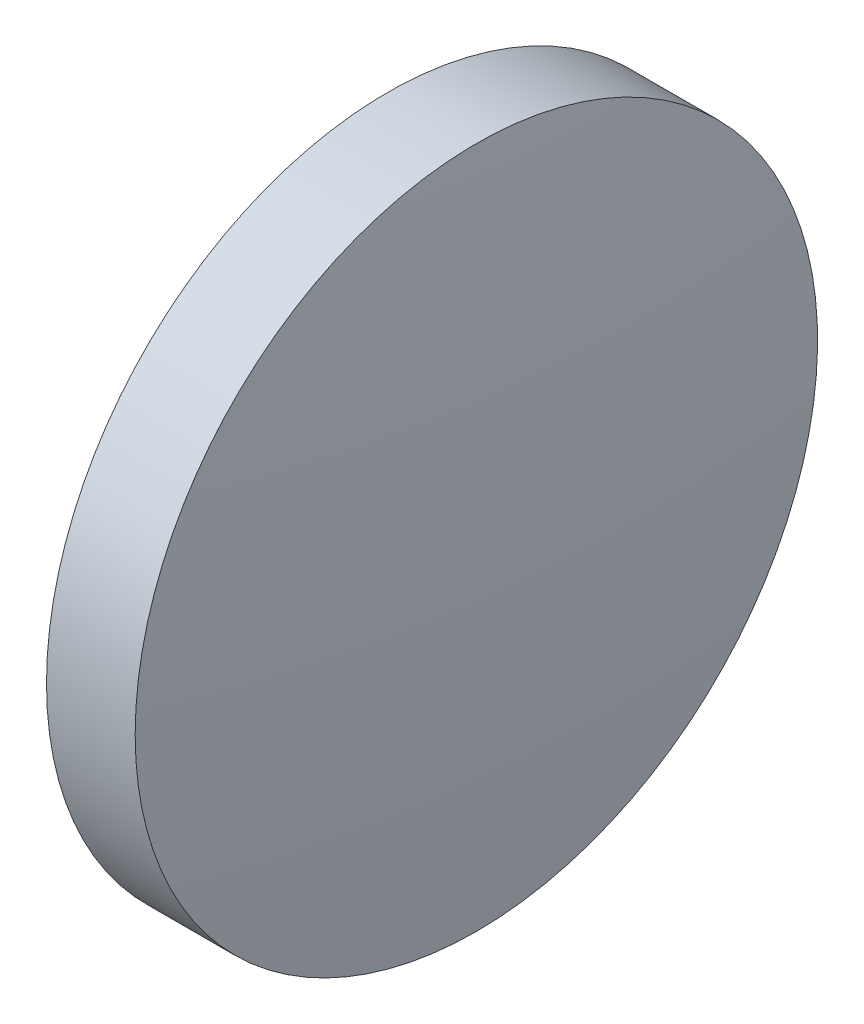
SolidWorks part; units mm, degrees
ref_plane "前视基准面" through (0, 0, 0) normal (0, 0, 1) x (1, 0, 0)
ref_plane "上视基准面" through (0, 0, 0) normal (0, 1, 0) x (1, 0, 0)
ref_plane "右视基准面" through (0, 0, 0) normal (1, 0, 0) x (0, 0, -1)
sketch "草图1" plane through (0, 0, 0) normal (0, 0, 1) x (1, 0, 0)
  line L0 (374.677, 118.3502) -> (393.473, 118.3502) construction
  line L1 (380.3069, 118.3502) -> (380.3069, 131.0502)
  line L2 (384.3069, 118.3502) -> (380.3069, 118.3502)
  line L5 (380.3069, 131.0502) -> (383.6069, 131.0502)
  arc A0 (384.3069, 118.3502) -> (383.6069, 131.0502) centre (268.7498, 118.3502) ccw
revolve "旋转1" add sketch "草图1" angle 360 about L0
